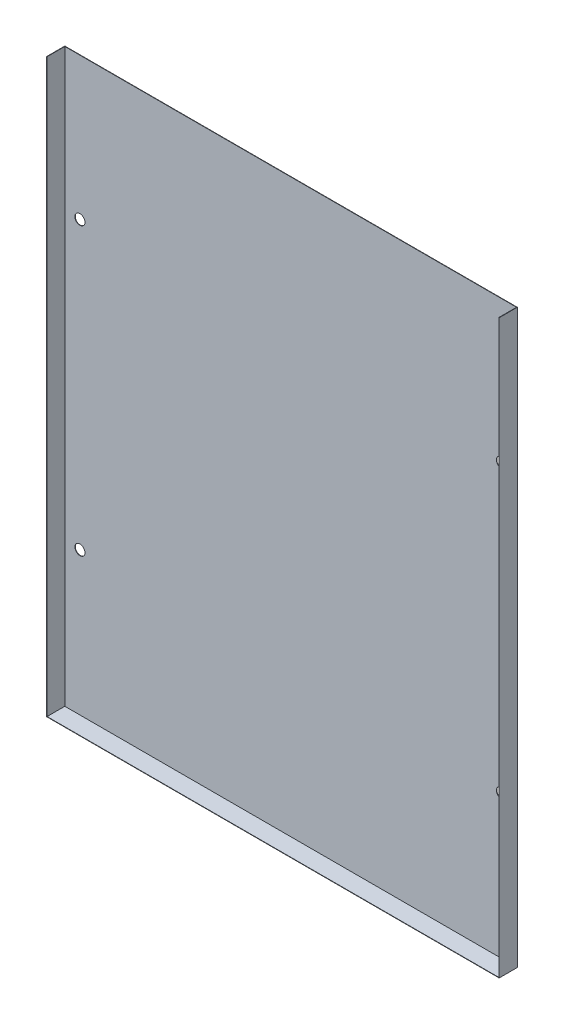
SolidWorks part; units mm, degrees
material "3003 Alloy"
ref_plane "Front Plane" through (0, 0, 0) normal (0, 0, 1) x (1, 0, 0)
ref_plane "Top Plane" through (0, 0, 0) normal (0, 1, 0) x (1, 0, 0)
ref_plane "Right Plane" through (0, 0, 0) normal (1, 0, 0) x (0, 0, -1)
sketch "Sketch1" plane through (0, 0, 0) normal (0, 0, 1) x (1, 0, 0)
  line L0 (-89.72, 113.5) -> (89.72, -113.5) construction
  line L1 (-89.72, -113.5) -> (89.72, -113.5)
  line L2 (-89.72, -113.5) -> (-89.72, 113.5)
  line L3 (-89.72, 113.5) -> (89.72, 113.5)
  line L4 (89.72, -113.5) -> (89.72, 113.5) construction
  line L5 (-83.72, 56.9786) -> (-83.72, -56.6738) construction
  line L6 (0, 113.5) -> (0, -113.5)
  circle A0 centre (-83.72, -56.6738) radius 2
  circle A1 centre (-83.72, 56.9786) radius 2
  dimension "D3" = 56.8262
  dimension "D5" = 6
  dimension "D6" = 4
  dimension "D7" = 4
  dimension "D1" = 179.44
  dimension "D2" = 227
  dimension "D4" = 170.4786
extrude "Heat Exchanger" add sketch "Sketch1" along normal blind 0.1524 contours L6 L3 L2 L1 A1 A0
sketch "Sketch3" plane through (0, 0, 0) normal (0, 0, 1) x (1, 0, 0)
  line L3 (0, -113.6524) -> (0, -113.5)
  line L5 (-89.8724, -113.6524) -> (0, -113.6524)
  line L6 (-89.8724, 113.5) -> (-89.8724, -113.6524)
  line L7 (-89.8724, -113.6524) -> (0, -113.6524)
  line L8 (-89.8724, 113.5) -> (-89.8724, -113.6524)
  line L9 (-89.8724, 113.5) -> (-89.72, 113.5)
  line L11 (-89.72, -113.5) -> (-89.72, 113.5) construction
  line L12 (-89.72, -113.5) -> (0, -113.5) construction
  line L13 (-89.72, -113.5) -> (-89.72, 113.5)
  line L14 (-89.72, -113.5) -> (0, -113.5)
  dimension "D1" = 0.1524
extrude "Convection Fin" add sketch "Sketch3" along normal blind 7.2048
mirror "Mirror1" about plane through (0, 0, 0) normal (1, 0, 0) of "Heat Exchanger", "Convection Fin"
